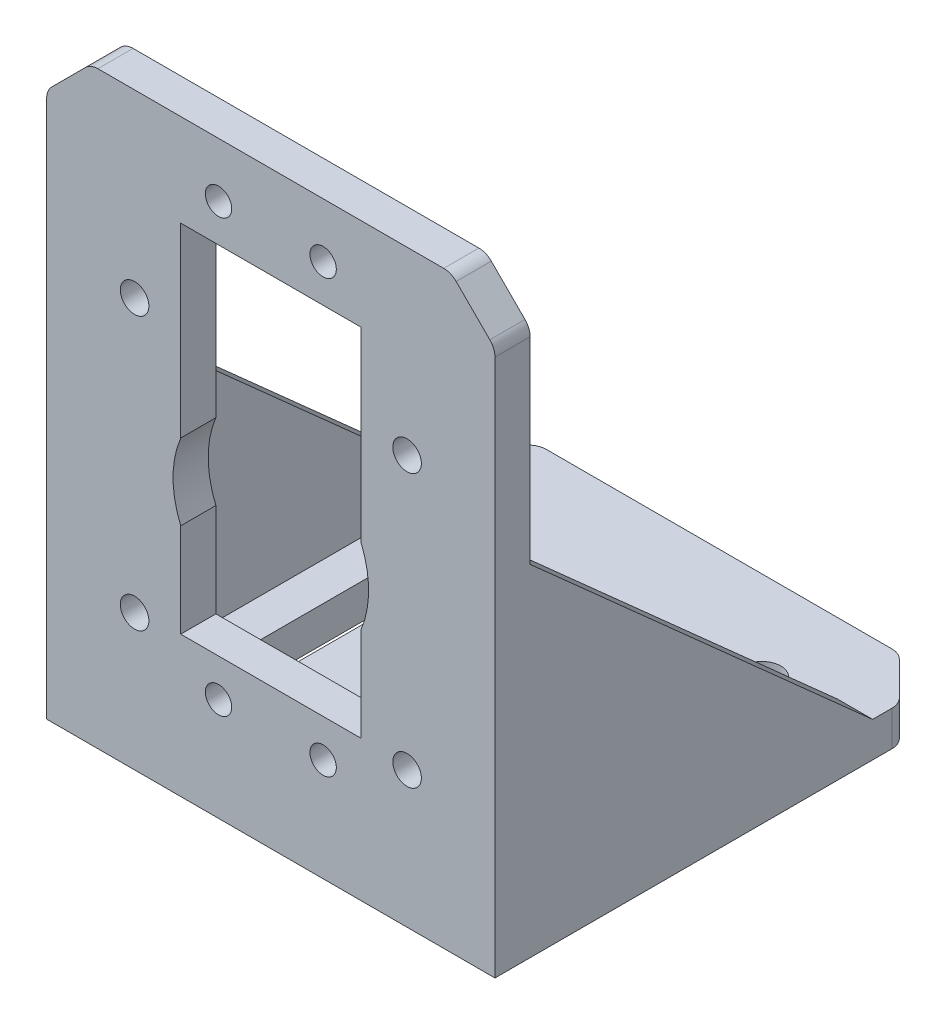
SolidWorks part; units mm, degrees
material "ABS"
ref_plane "Front Plane" through (0, 0, 0) normal (0, 0, 1) x (1, 0, 0)
ref_plane "Top Plane" through (0, 0, 0) normal (0, 1, 0) x (1, 0, 0)
ref_plane "Right Plane" through (0, 0, 0) normal (1, 0, 0) x (0, 0, -1)
sketch "Sketch1" plane through (0, 0, 0) normal (1, 0, 0) x (0, 0, -1)
  line L0 (0, 0) -> (0, 67)
  line L1 (0, 67) -> (4, 67)
  line L2 (4, 67) -> (4, 4)
  line L3 (4, 4) -> (51, 4)
  line L4 (51, 4) -> (51, 0)
  line L5 (51, 0) -> (0, 0)
  dimension "D1" = 67
  dimension "D2" = 51
  dimension "D3" = 4
  dimension "D4" = 4
extrude "Boss-Extrude1" add sketch "Sketch1" along normal blind 51
sketch "Sketch2" plane through (0, 0, 0) normal (0, 0, 1) x (1, 0, 0)
  line L0 (51, 67) -> (0, 67) construction
  line L3 (51, 4) -> (0, 4) construction
  circle A0 centre (25.5, 31) radius 11.125
  point P4 (25.5, 67)
  dimension "D1" = 22.25
  dimension "D2" = 27
sketch "Sketch3" plane through (0, 4, 0) normal (0, 1, 0) x (1, 0, 0)
  line L0 (10.49, 51) -> (10.49, 11.15) construction
  line L1 (51, 51) -> (0, 51) construction
  line L2 (51, 4) -> (0, 4) construction
  line L3 (42.66, 11.15) -> (51, 11.15) construction
  line L4 (40.51, 4) -> (40.51, 11.15) construction
  line L5 (51, 51) -> (51, 4) construction
  line L6 (0, 51) -> (0, 4) construction
  line L7 (8.34, 40.85) -> (8.34, 11.15)
  line L8 (0, 11.15) -> (8.34, 11.15) construction
  line L9 (38.36, 40.85) -> (38.36, 11.15)
  line L10 (12.64, 11.15) -> (12.64, 40.85)
  line L12 (42.66, 11.15) -> (42.66, 40.85)
  line L13 (40.51, 13.3) -> (40.51, 37.5958) construction
  line L14 (12.64, 11.15) -> (38.36, 11.15) construction
  line L15 (10.49, 9) -> (10.49, 4) construction
  arc A0 (12.64, 40.85) -> (8.34, 40.85) centre (10.49, 40.85) ccw
  arc A1 (42.66, 40.85) -> (38.36, 40.85) centre (40.51, 40.85) ccw
  arc A2 (8.34, 11.15) -> (12.64, 11.15) centre (10.49, 11.15) ccw
  arc A3 (38.36, 11.15) -> (42.66, 11.15) centre (40.51, 11.15) ccw
  dimension "D5" = 4.3
  dimension "D2" = 7.15
  dimension "D3" = 10.49
  dimension "D4" = 10.49
extrude "Cut-Extrude2" cut sketch "Sketch3" against normal blind 51
sketch "Sketch4" plane through (0, 0, 0) normal (0, 0, 1) x (1, 0, 0)
  line L0 (51, 15.5) -> (0, 15.5) construction
  line L1 (51, 67) -> (51, 0) construction
  line L2 (0, 67) -> (0, 0) construction
  line L3 (51, 46.5) -> (0, 46.5) construction
  line L4 (51, 4) -> (0, 4) construction
  line L6 (10, 67) -> (10, 4) construction
  line L7 (51, 67) -> (0, 67) construction
  line L8 (41, 67) -> (41, 4) construction
  circle A0 centre (10, 46.5) radius 1.625
  circle A1 centre (41, 46.5) radius 1.625
  circle A2 centre (41, 15.5) radius 1.625
  circle A3 centre (10, 15.5) radius 1.625
  dimension "D6" = 3.25
  dimension "D1" = 11.5
  dimension "D2" = 31
  dimension "D3" = 10
  dimension "D4" = 31
  dimension "D5" = 63
extrude "Cut-Extrude3" cut sketch "Sketch4" against normal blind 51
chamfer "Chamfer1" distance 5 angle 45 4 edges at (0, 2, -51) (51, 2, -51) (51, 67, -2) (0, 67, -2)
fillet "Fillet1" radius 2 8 edges at (51, 2, -46) (51, 62, -2) (46, 67, -2) (5, 67, -2) (0, 62, -2) (0, 2, -46) (5, 2, -51) (46, 2, -51)
sketch "Sketch5" plane through (0, 0, -4) normal (0, 0, -1) x (-1, 0, 0)
  line L0 (-8.375, 46.5) -> (-51, 46.5) construction
  line L1 (-35.75, 56.5) -> (-15.25, 56.5)
  line L2 (-35.75, 56.5) -> (-35.75, 16)
  line L3 (-35.75, 16) -> (-15.25, 16)
  line L4 (-15.25, 56.5) -> (-15.25, 16)
  line L6 (-25.5, 67) -> (-25.5, 0) construction
  line L7 (-51, 4) -> (-51, 61.1716) construction
  line L8 (-45.1716, 67) -> (-5.8284, 67) construction
  line L9 (-45.1716, 0) -> (-5.8284, 0) construction
  circle A0 centre (-10, 46.5) radius 1.625 construction
  point P0 (-25.5, 46.5)
  point P19 (-25.5, 56.5)
  dimension "D1" = 20.5
  dimension "D2" = 10
  dimension "D3" = 40.5
extrude "Cut-Extrude4" cut sketch "Sketch5" against normal blind 10
sketch "Sketch6" plane through (51, 0, 0) normal (1, 0, 0) x (0, 0, -1)
  line L0 (4, 38.751) -> (42.9661, 4)
  line L1 (4, 4) -> (4, 61.1716) construction
  line L2 (45.1716, 4) -> (4, 4) construction
rib "Rib1" sketch "Sketch6" sketch "Sketch6" thickness 4 extrusion direction parallel to sketch draft on no parameters "D1"=4
ref_plane "Plane2" through (25.5, 0, 0) normal (-1, 0, 0) x (0, 0, 1)
mirror "Mirror1" about plane through (25.5, 0, 0) normal (-1, 0, 0) of "Rib1"
sketch "Sketch7" plane through (0, 0, -4) normal (0, 0, -1) x (-1, 0, 0)
  line L0 (-15.25, 56.5) -> (-35.75, 56.5) construction
  line L1 (-35.75, 56.5) -> (-35.75, 16) construction
  line L2 (-15.25, 16) -> (-15.25, 56.5) construction
  line L3 (-31.45, 60.8) -> (-31.45, 11.7) construction
  circle A0 centre (-31.45, 60.8) radius 1.5
  circle A1 centre (-19.55, 60.8) radius 1.5
  circle A2 centre (-31.45, 11.7) radius 1.5
  circle A3 centre (-19.55, 11.7) radius 1.5
  dimension "D1" = 3
  dimension "D2" = 3
  dimension "D3" = 4.3
  dimension "D4" = 4.3
  dimension "D5" = 4.3
  dimension "D6" = 4.3
  dimension "D7" = 49.1
extrude "Cut-Extrude5" cut sketch "Sketch7" against normal blind 10
extrude "Cut-Extrude6" cut sketch "Sketch2" against normal blind 10
